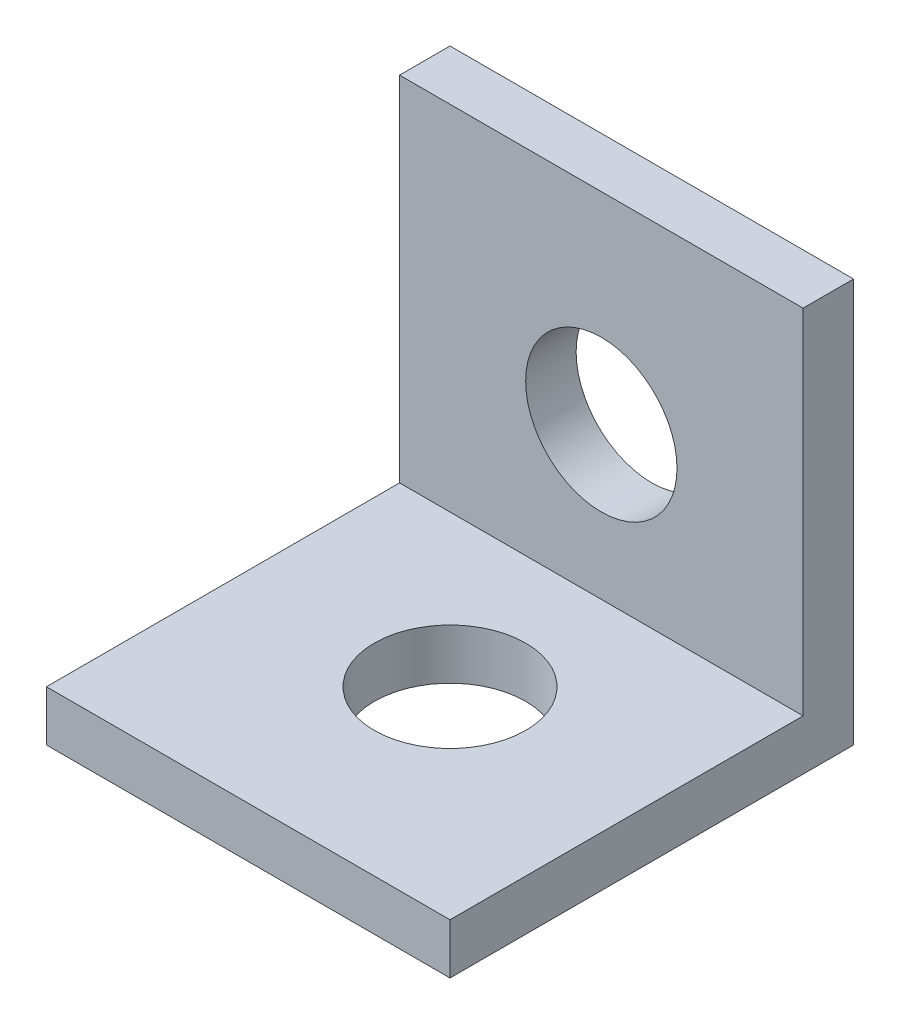
SolidWorks part; units mm, degrees
ref_plane "Front Plane" through (0, 0, 0) normal (0, 0, 1) x (1, 0, 0)
ref_plane "Top Plane" through (0, 0, 0) normal (0, 1, 0) x (1, 0, 0)
ref_plane "Right Plane" through (0, 0, 0) normal (1, 0, 0) x (0, 0, -1)
sketch "Sketch1" plane through (0, 0, 0) normal (1, 0, 0) x (0, 0, -1)
  line L0 (0, 0) -> (-25.4, 0)
  line L1 (-25.4, 0) -> (-25.4, 3.175)
  line L2 (-25.4, 3.175) -> (-3.175, 3.175)
  line L3 (-3.175, 3.175) -> (-3.175, 25.4)
  line L4 (-3.175, 25.4) -> (0, 25.4)
  line L5 (0, 25.4) -> (0, 0)
  dimension "D1" = 25.4
  dimension "D2" = 3.175
  dimension "D3" = 90
extrude "Boss-Extrude1" add sketch "Sketch1" along normal blind 25.4
sketch "Sketch2" plane through (0, 3.175, 0) normal (0, 1, 0) x (1, 0, 0)
  line L0 (12.7, -25.4) -> (12.7, -12.7) construction
  line L1 (25.4, -25.4) -> (0, -25.4) construction
  circle A0 centre (12.7, -12.7) radius 4.7625
  dimension "D1" = 9.525
  dimension "D2" = 12.7
extrude "Cut-Extrude1" cut sketch "Sketch2" against normal blind 25.4
sketch "Sketch3" plane through (0, 0, 3.175) normal (0, 0, 1) x (1, 0, 0)
  line L0 (12.7, 25.4) -> (12.7, 12.7) construction
  line L1 (25.4, 25.4) -> (0, 25.4) construction
  circle A0 centre (12.7, 12.7) radius 4.7625
  dimension "D1" = 9.525
  dimension "D2" = 12.7
extrude "Cut-Extrude2" cut sketch "Sketch3" against normal through all
